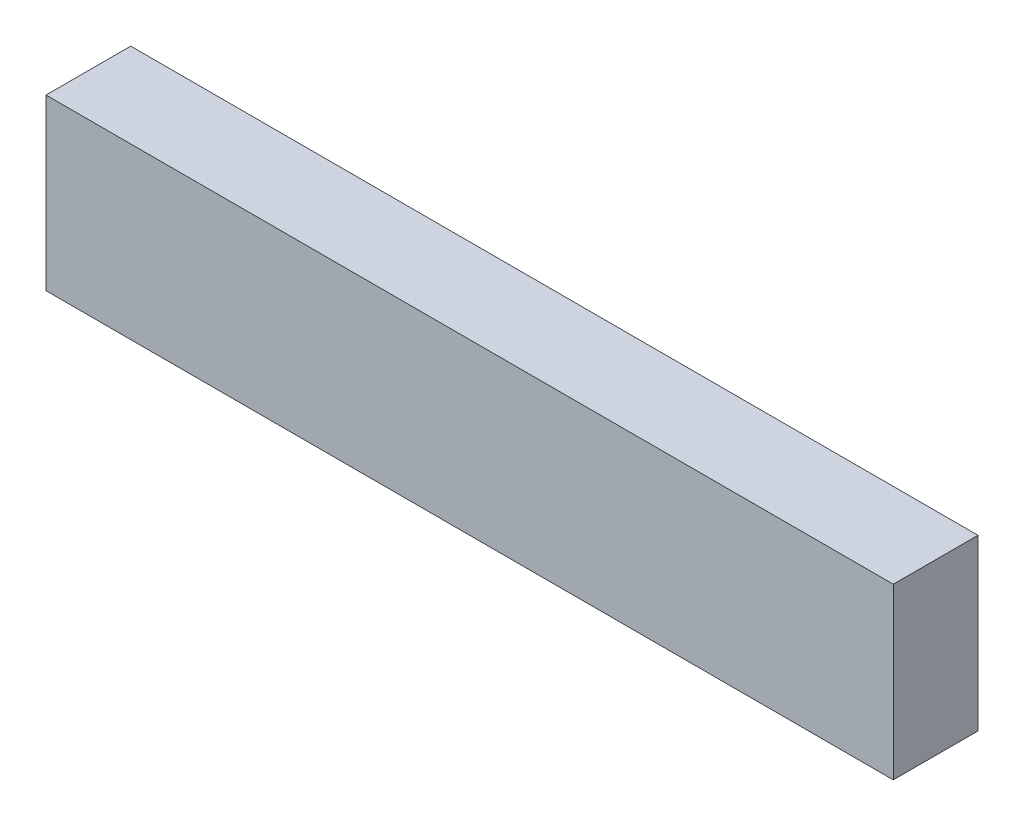
SolidWorks part; units mm, degrees
ref_plane "Plan de face" through (0, 0, 0) normal (0, 0, 1) x (1, 0, 0)
ref_plane "Plan de dessus" through (0, 0, 0) normal (0, 1, 0) x (1, 0, 0)
ref_plane "Plan de droite" through (0, 0, 0) normal (1, 0, 0) x (0, 0, -1)
sketch "Esquisse1" plane through (0, 0, 0) normal (0, 0, 1) x (1, 0, 0)
  line L1 (0, 0) -> (100, 0)
  line L2 (0, 0) -> (0, 20)
  line L3 (0, 20) -> (100, 20)
  line L4 (100, 0) -> (100, 20)
  dimension "D1" = 100
  dimension "D2" = 20
extrude "Boss.-Extru.1" add sketch "Esquisse1" along normal blind 10
